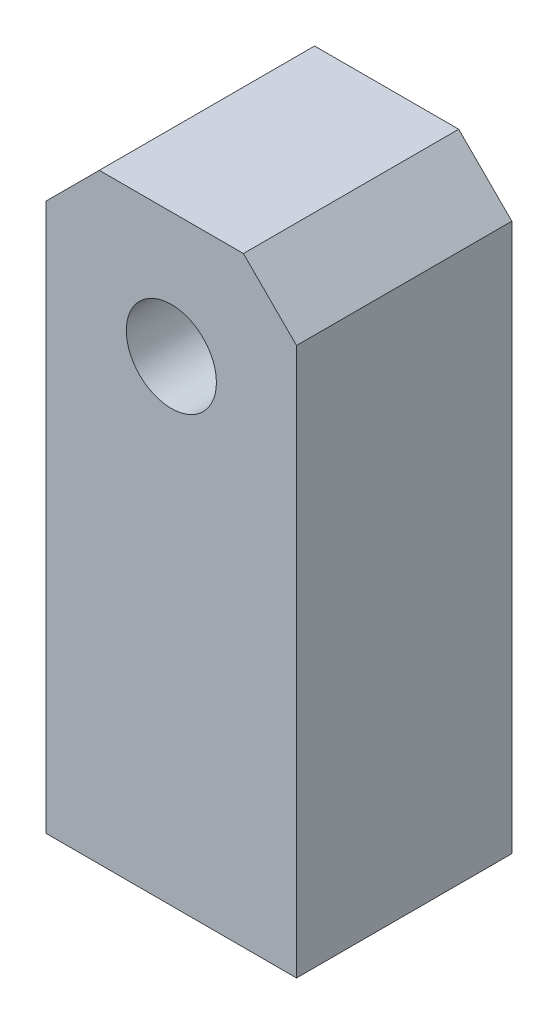
SolidWorks part; units mm, degrees
ref_plane "Front Plane" through (0, 0, 0) normal (0, 0, 1) x (1, 0, 0)
ref_plane "Top Plane" through (0, 0, 0) normal (0, 1, 0) x (1, 0, 0)
ref_plane "Right Plane" through (0, 0, 0) normal (1, 0, 0) x (0, 0, -1)
sketch "Sketch1" plane through (0, 0, 0) normal (0, 0, 1) x (1, 0, 0)
  line L0 (1.4393, 2.5) -> (2.5, 1.4393)
  line L1 (-2.5, 2.5) -> (2.5, 2.5)
  line L2 (-2.5, 2.5) -> (-2.5, -9.5)
  line L3 (-2.5, -9.5) -> (2.5, -9.5)
  line L4 (2.5, 2.5) -> (2.5, -9.5)
  line L5 (-2.5, 1.4393) -> (-1.4393, 2.5)
  circle A0 centre (0, 0) radius 0.9
  point P4 (0, 2.5)
  dimension "D3" = 1.8
  dimension "D1" = 5
  dimension "D2" = 12
  dimension "D4" = 2.5
  dimension "D5" = 1.5
  dimension "D6" = 45
extrude "Boss-Extrude1" add sketch "Sketch1" along normal blind 4.3 contours L5 L2 L3 L4 L0 L1 A0
